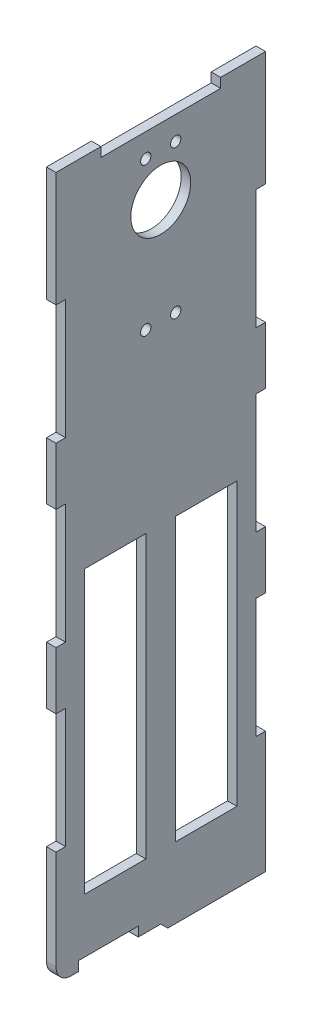
SolidWorks part; units mm, degrees
ref_plane "Front Plane" through (0, 0, 0) normal (0, 0, 1) x (1, 0, 0)
ref_plane "Top Plane" through (0, 0, 0) normal (0, 1, 0) x (1, 0, 0)
ref_plane "Right Plane" through (0, 0, 0) normal (1, 0, 0) x (0, 0, -1)
sketch "Sketch1" plane through (0, 0, 0) normal (0, 0, 1) x (1, 0, 0)
  line L0 (-0.0791, 56.9548) -> (37.9209, 56.9548)
  line L1 (-41.3824, -107.3021) -> (-5.8824, -107.3021)
  line L2 (-41.3824, -107.3021) -> (-41.3824, -92.3021)
  line L3 (-41.3824, -92.3021) -> (-5.8824, -92.3021)
  line L4 (-5.8824, -107.3021) -> (-5.8824, -92.3021)
  line L5 (2.6358, -107.3021) -> (38.1358, -107.3021)
  line L6 (2.6358, -107.3021) -> (2.6358, -92.3021)
  line L7 (2.6358, -92.3021) -> (38.1358, -92.3021)
  line L8 (38.1358, -107.3021) -> (38.1358, -92.3021)
  line L9 (-24.6576, 14.9093) -> (-7.6576, 14.9093)
  line L10 (-24.6576, 14.9093) -> (-24.6576, 40.9093)
  line L11 (-24.6576, 40.9093) -> (-7.6576, 40.9093)
  line L12 (-7.6576, 14.9093) -> (-7.6576, 40.9093)
  line L13 (-24.6576, 14.9093) -> (-7.6576, 40.9093) construction
  line L14 (-24.6576, 40.9093) -> (-7.6576, 14.9093) construction
  line L15 (-1.5747, 14.9093) -> (15.4253, 14.9093)
  line L16 (-1.5747, 14.9093) -> (-1.5747, 40.9093)
  line L17 (-1.5747, 40.9093) -> (15.4253, 40.9093)
  line L18 (15.4253, 14.9093) -> (15.4253, 40.9093)
  line L19 (-1.5747, 14.9093) -> (15.4253, 40.9093) construction
  line L20 (-1.5747, 40.9093) -> (15.4253, 14.9093) construction
  line L21 (-41.6576, -76.0402) -> (9.3424, -76.0402)
  line L22 (-41.6576, -76.0402) -> (-41.6576, 4.9598)
  line L23 (-41.6576, 4.9598) -> (9.3424, 4.9598)
  line L24 (9.3424, -76.0402) -> (9.3424, 4.9598)
  line L25 (-41.6576, -76.0402) -> (9.3424, 4.9598) construction
  line L26 (-41.6576, 4.9598) -> (9.3424, -76.0402) construction
  line L27 (-19.9076, -76.1058) -> (38.5924, -76.1058)
  line L28 (-19.9076, -76.1058) -> (-19.9076, 10.9942)
  line L29 (-19.9076, 10.9942) -> (38.5924, 10.9942)
  line L30 (38.5924, -76.1058) -> (38.5924, 10.9942)
  line L31 (-19.9076, -76.1058) -> (38.5924, 10.9942) construction
  line L32 (-19.9076, 10.9942) -> (38.5924, -76.1058) construction
  line L33 (-40.4187, 56.9548) -> (-2.4187, 56.9548)
  line L34 (-40.4187, 56.9548) -> (-40.4187, 106.4548)
  line L35 (-40.4187, 106.4548) -> (-2.4187, 106.4548)
  line L36 (-2.4187, 56.9548) -> (-2.4187, 106.4548)
  line L37 (-40.4187, 56.9548) -> (-2.4187, 106.4548) construction
  line L38 (-40.4187, 106.4548) -> (-2.4187, 56.9548) construction
  line L39 (-0.0791, 56.9548) -> (-0.0791, 106.4548)
  line L40 (-0.0791, 106.4548) -> (37.9209, 106.4548)
  line L41 (37.9209, 56.9548) -> (37.9209, 106.4548)
  line L42 (-0.0791, 56.9548) -> (37.9209, 106.4548) construction
  line L43 (-0.0791, 106.4548) -> (37.9209, 56.9548) construction
  line L44 (-50, 117.5) -> (50, -117.5) construction
  line L45 (-50, -117.5) -> (50, -117.5)
  line L46 (-50, -117.5) -> (-50, 117.5)
  line L47 (-50, 117.5) -> (50, 117.5)
  line L48 (50, -117.5) -> (50, 117.5)
  point P8 (-16.1576, 27.9093)
  point P13 (6.9253, 27.9093)
  point P19 (18.9209, 81.7048)
  point P20 (9.3424, -32.5558)
  point P26 (-21.4187, 81.7048)
  point P28 (-16.1576, -35.5402)
  dimension "D1" = 15
  dimension "D2" = 35.5
  dimension "D3" = 17
  dimension "D4" = 26
  dimension "D5" = 51
  dimension "D6" = 81
  dimension "D7" = 87.1
  dimension "D8" = 58.5
  dimension "D9" = 49.5
  dimension "D10" = 38
  dimension "D11" = 100
  dimension "D12" = 235
sketch "Sketch2" plane through (0, 0, 0) normal (1, 0, 0) x (0, 0, -1)
  line L0 (35, -114.325) -> (-35, -114.325) construction
  line L1 (35, -117.5) -> (-35, -117.5)
  line L2 (35, -117.5) -> (35, 117.5)
  line L3 (35, 117.5) -> (-35, 117.5)
  line L4 (-35, -117.5) -> (-35, 117.5)
  line L5 (35, -117.5) -> (-35, 117.5) construction
  line L6 (35, 117.5) -> (-35, -117.5) construction
  line L7 (10, 56.9548) -> (-10, 56.9548)
  line L8 (10, 56.9548) -> (10, 106.4548)
  line L9 (10, 106.4548) -> (-10, 106.4548)
  line L10 (-10, 56.9548) -> (-10, 106.4548)
  line L11 (10, 56.9548) -> (-10, 106.4548) construction
  line L12 (10, 106.4548) -> (-10, 56.9548) construction
  line L13 (25, 14.9093) -> (-25, 14.9093)
  line L14 (25, 14.9093) -> (25, 40.9093)
  line L15 (25, 40.9093) -> (-25, 40.9093)
  line L16 (-25, 14.9093) -> (-25, 40.9093)
  line L17 (25, 14.9093) -> (-25, 40.9093) construction
  line L18 (25, 40.9093) -> (-25, 14.9093) construction
  line L19 (-5.5, -114.325) -> (-25.5, -114.325)
  line L20 (-5.5, -114.325) -> (-5.5, -99.325)
  line L21 (-5.5, -99.325) -> (-25.5, -99.325)
  line L22 (-25.5, -114.325) -> (-25.5, -99.325)
  line L23 (25.475, -94.15) -> (10.475, -94.15)
  line L24 (25.475, -94.15) -> (25.475, -7.05)
  line L25 (25.475, -7.05) -> (10.475, -7.05)
  line L26 (10.475, -94.15) -> (10.475, -7.05)
  line L27 (-8.8818, -94.15) -> (-23.8818, -94.15)
  line L28 (-8.8818, -94.15) -> (-8.8818, -13.15)
  line L29 (-8.8818, -13.15) -> (-23.8818, -13.15)
  line L30 (-23.8818, -94.15) -> (-23.8818, -13.15)
  line L31 (-15.5, -99.325) -> (-15.5, -114.325) construction
  line L32 (2.325, -117.5) -> (2.325, -119.825)
  line L33 (2.325, -119.825) -> (35, -119.825)
  line L34 (-31.825, -117.5) -> (-31.825, 117.5) construction
  line L36 (31.825, -117.5) -> (31.825, 117.5) construction
  line L37 (35, -117.5) -> (35, -119.825)
  line L38 (-2.1092, -99.325) -> (-2.1092, -96.15)
  line L39 (-31.825, -99.325) -> (31.825, -99.325)
  line L40 (-31.825, -99.325) -> (-31.825, -96.15)
  line L41 (-31.825, -96.15) -> (31.825, -96.15)
  line L42 (31.825, -99.325) -> (31.825, -96.15)
  line L43 (-27.9557, -99.325) -> (-27.9557, -96.15)
  line L44 (0, -117.5) -> (0, 117.5) construction
  line L45 (31.825, 11.7343) -> (-31.825, 11.7343)
  line L46 (31.825, 11.7343) -> (31.825, 14.9093)
  line L47 (31.825, 14.9093) -> (-31.825, 14.9093)
  line L48 (-31.825, 11.7343) -> (-31.825, 14.9093)
  line L49 (31.825, 40.9093) -> (-31.825, 40.9093)
  line L50 (31.825, 40.9093) -> (31.825, 44.0843)
  line L51 (31.825, 44.0843) -> (-31.825, 44.0843)
  line L52 (-31.825, 40.9093) -> (-31.825, 44.0843)
  line L53 (5, -1.9843) -> (5, -96.15)
  line L54 (25.475, -96.15) -> (-25.475, -96.15)
  line L55 (25.475, -96.15) -> (25.475, -1.9843)
  line L56 (25.475, -1.9843) -> (-25.475, -1.9843)
  line L57 (-25.475, -96.15) -> (-25.475, -1.9843)
  line L58 (-5, -1.9843) -> (-5, -96.15)
  line L59 (2.325, -119.825) -> (0, -117.5)
  line L60 (10, 61.3048) -> (-10, 61.3048) construction
  line L61 (10, 61.3048) -> (10, 102.1048)
  line L62 (10, 102.1048) -> (-10, 102.1048) construction
  line L63 (-10, 61.3048) -> (-10, 102.1048)
  line L64 (10, 61.3048) -> (-10, 102.1048) construction
  line L65 (10, 102.1048) -> (-10, 61.3048) construction
  circle A0 centre (-15.5, -106.825) radius 13
  circle A1 centre (5, 106.4548) radius 1.725
  circle A2 centre (-5, 106.4548) radius 1.725
  circle A3 centre (5, 56.9548) radius 1.725
  circle A4 centre (-5, 56.9548) radius 1.725
  circle A5 centre (0, 92.1048) radius 10
  point P0 (0, 0)
  point P6 (0, 81.7048)
  point P12 (0, 27.9093)
  point P43 (0, 81.7048)
  dimension "D14" = 26
  dimension "D23" = 3.45
  dimension "D1" = 235
  dimension "D2" = 70
  dimension "D3" = 20
  dimension "D4" = 49.5
  dimension "D5" = 50
  dimension "D6" = 26
  dimension "D7" = 15
  dimension "D8" = 20
  dimension "D9" = 15
  dimension "D10" = 87.1
  dimension "D11" = 15
  dimension "D12" = 81
  dimension "D16" = 19.5
  dimension "D17" = 40.8
  dimension "D19" = 3.175
  dimension "D20" = 6.35
  dimension "D21" = 2
  dimension "D22" = 3.175
  dimension "D24" = 10
  dimension "D25" = 5
  dimension "D26" = 6.35
  dimension "D28" = 5
  dimension "D29" = 45
  dimension "D13" = 3.175
  dimension "D15" = 3.175
  dimension "D18" = 3.175
  dimension "D27" = 10
extrude "Boss-Extrude1" add sketch "Sketch2" along normal blind 3.175
sketch "Sketch3" plane through (0, 0, 0) normal (-1, 0, 0) x (0, 0, 1)
  line L0 (-35, 0) -> (35, 0) construction
  line L1 (35, -117.5) -> (35, 117.5) construction
  line L2 (0, 0) -> (0, 118.3106) construction
  line L3 (-35, 59.1553) -> (35, 59.1553) construction
  line L4 (-31.825, 79.1553) -> (-38.175, 39.1553) construction
  line L5 (31.825, 39.1553) -> (38.175, 39.1553)
  line L6 (31.825, 39.1553) -> (31.825, 79.1553)
  line L7 (31.825, 79.1553) -> (38.175, 79.1553)
  line L8 (38.175, 39.1553) -> (38.175, 79.1553)
  line L9 (31.825, 39.1553) -> (38.175, 79.1553) construction
  line L10 (31.825, 79.1553) -> (38.175, 39.1553) construction
  line L11 (35, 0) -> (31.825, 0)
  line L12 (35, -20) -> (35, 20)
  line L13 (35, 20) -> (31.825, 20)
  line L14 (31.825, -20) -> (31.825, 20)
  line L15 (-31.825, 39.1553) -> (-38.175, 79.1553) construction
  line L16 (-31.825, -20) -> (-31.825, 20)
  line L17 (-35, 20) -> (-31.825, 20)
  line L18 (-35, -20) -> (-35, 20)
  line L19 (-35, 0) -> (-31.825, 0)
  line L20 (-38.175, 39.1553) -> (-38.175, 79.1553)
  line L21 (-31.825, 79.1553) -> (-38.175, 79.1553)
  line L22 (-31.825, 39.1553) -> (-31.825, 79.1553)
  line L23 (-31.825, 39.1553) -> (-38.175, 39.1553)
  line L24 (-31.825, -39.1553) -> (-38.175, -79.1553) construction
  line L25 (31.825, -79.1553) -> (38.175, -39.1553) construction
  line L26 (31.825, -39.1553) -> (38.175, -79.1553) construction
  line L27 (-31.825, -79.1553) -> (-38.175, -39.1553) construction
  line L28 (-35, -59.1553) -> (35, -59.1553) construction
  line L29 (-31.825, -39.1553) -> (-38.175, -39.1553)
  line L30 (-31.825, -39.1553) -> (-31.825, -79.1553)
  line L31 (-31.825, -79.1553) -> (-38.175, -79.1553)
  line L32 (-38.175, -39.1553) -> (-38.175, -79.1553)
  line L33 (-35, -20) -> (-31.825, -20)
  line L34 (35, -20) -> (31.825, -20)
  line L35 (38.175, -39.1553) -> (38.175, -79.1553)
  line L36 (31.825, -79.1553) -> (38.175, -79.1553)
  line L37 (31.825, -39.1553) -> (31.825, -79.1553)
  line L38 (31.825, -39.1553) -> (38.175, -39.1553)
  line L39 (-35, 117.5) -> (35, 117.5) construction
  line L40 (-20, 114.325) -> (20, 114.325)
  line L41 (-20, 114.325) -> (-20, 122.2962)
  line L42 (-20, 122.2962) -> (20, 122.2962)
  line L43 (20, 114.325) -> (20, 122.2962)
  line L44 (-20, 114.325) -> (20, 122.2962) construction
  line L45 (-20, 122.2962) -> (20, 114.325) construction
  line L46 (0, -117.5) -> (35, -117.5) construction
  line L47 (7.5, -120.675) -> (27.5, -120.675)
  line L48 (7.5, -120.675) -> (7.5, -114.325)
  line L49 (7.5, -114.325) -> (27.5, -114.325)
  line L50 (27.5, -120.675) -> (27.5, -114.325)
  line L51 (7.5, -120.675) -> (27.5, -114.325) construction
  line L52 (7.5, -114.325) -> (27.5, -120.675) construction
  point P20 (0, 59.1553)
  point P38 (0, -59.1553)
  point P45 (17.5, -117.5)
  line M14 (0, -117.5) -> (35, -117.5)
  line M16 (35, -117.5) -> (35, 117.5)
  line M17 (35, 117.5) -> (-35, 117.5)
  line M18 (-35, 117.5) -> (-35, -119.825)
  dimension "D1" = 3.175
  dimension "D2" = 40
  dimension "D3" = 20
  dimension "D4" = 40
  dimension "D5" = 3.175
  dimension "D6" = 20
  dimension "D7" = 3.175
extrude "Cut-Extrude1" cut sketch "Sketch3" against normal blind 10 contours L23 L22 L21 M18 | L7 L6 L5 M16 | L14 L11 L13 M16 | L19 L16 L17 M18 | L18 L33 L16 L19 | L34 L11 L14 M16 | L38 L37 L36 M16 | L31 L30 L29 M18 | L40 L43 L41 M17 | L50 L49 L48 M14
fillet "Fillet1" radius 5 1 edges at (1.5875, -117.5, 35)
